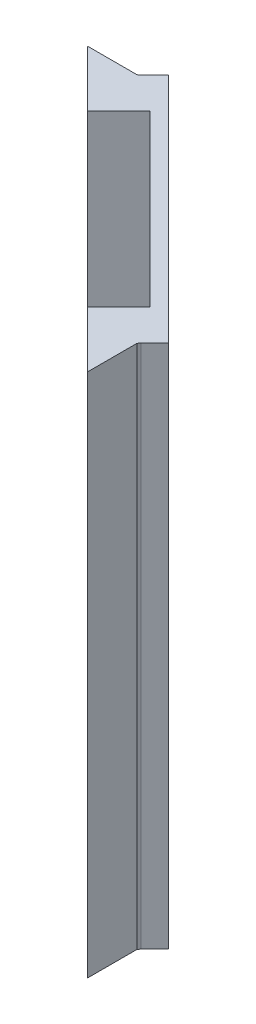
SolidWorks part; units mm, degrees
ref_plane "Front Plane" through (0, 0, 0) normal (0, 0, 1) x (1, 0, 0)
ref_plane "Top Plane" through (0, 0, 0) normal (0, 1, 0) x (1, 0, 0)
ref_plane "Right Plane" through (0, 0, 0) normal (1, 0, 0) x (0, 0, -1)
sketch "Sketch1" plane through (0, 0, 0) normal (0, 1, 0) x (1, 0, 0)
  line L1 (53.7307, 35.7377) -> (89.086, 0.3824) construction
  line L3 (89.086, -49.6176) -> (-36.2693, -49.6176) construction
  line L4 (-36.2693, -49.6176) -> (-36.2693, 35.7377) construction
  line L5 (-39.2693, -52.6176) -> (-39.2693, 38.7377) construction
  line L6 (-39.2693, 38.7377) -> (54.9733, 38.7377) construction
  line L7 (54.9733, 38.7377) -> (92.086, 1.625) construction
  line L8 (92.086, 1.625) -> (92.086, -52.6176) construction
  line L9 (92.086, -52.6176) -> (-39.2693, -52.6176) construction
  line L10 (53.7307, 35.7377) -> (55.852, 37.859) construction
  line L11 (89.086, 0.3824) -> (91.2073, 2.5037) construction
  line L12 (49.3113, 31.6718) -> (89.086, -8.1029) construction
  line L13 (53.3771, 35.7377) -> (55.6752, 38.0358) construction
  line L14 (55.6752, 38.0358) -> (54.9733, 38.7377) construction
  line L15 (91.2073, 2.5037) -> (92.086, 1.625) construction
  line L16 (89.086, 0.0288) -> (91.3841, 2.3269) construction
  line L17 (85.1969, -8.4565) -> (44.8918, 31.8486) construction
  line L18 (-36.2693, 35.7377) -> (53.3771, 35.7377) construction
  line L19 (-36.2693, 35.7377) -> (53.7307, 35.7377) construction
  line L20 (89.086, -49.6176) -> (89.086, 0.0288) construction
  line L21 (89.086, 0.3824) -> (89.086, -49.6176) construction
  line L22 (44.8918, 31.8486) -> (50.7255, 26.015) construction
  line L23 (50.7255, 26.015) -> (52.8468, 28.1363) construction
  line L24 (52.8468, 28.1363) -> (49.3113, 31.6718) construction
  line L25 (53.3771, 35.7377) -> (49.3113, 31.6718) construction
  line L26 (85.1969, -8.4565) -> (79.363, -2.6225) construction
  line L27 (79.363, -2.6225) -> (81.4843, -0.5012) construction
  line L28 (85.0198, -4.0367) -> (81.4843, -0.5012) construction
  line L29 (89.086, -8.1029) -> (89.086, 0.0288) construction
  line L30 (89.086, 0.0288) -> (85.0198, -4.0367) construction
  line L31 (49.3113, 31.6718) -> (45.2454, 35.7377) construction
  line L32 (44.8918, 31.8486) -> (51.0028, 35.7377) construction
  line L33 (85.1969, -8.4565) -> (89.086, -12.3456) construction
  line L34 (85.0198, -4.0367) -> (89.086, -8.1029) construction
  line L35 (-36.2693, 24.0809) -> (-24.6125, 35.7377) construction
  line L36 (50.7255, 26.015) -> (9.8915, 35.7377) construction
  line L37 (35.7601, 35.7377) -> (35.7601, 29.5783) construction
  line L38 (35.7601, 29.5783) -> (50.7255, 26.015) construction
  line L39 (-36.2693, -37.9608) -> (-24.6125, -49.6176) construction
  line L40 (73.5297, 20.1814) -> (65.0444, 11.6961) construction
  line L41 (89.086, -17.5882) -> (82.9266, -17.5882) construction
  line L42 (82.9266, -17.5882) -> (79.3633, -2.6228) construction
  line L43 (26.4084, -52.6176) -> (26.4084, 38.7377) construction
  line L44 (89.086, -37.9608) -> (77.4292, -49.6176) construction
  line L45 (89.086, 0.3824) -> (91.2073, 2.5037)
  line L46 (91.2073, 2.5037) -> (55.852, 37.859)
  line L47 (55.852, 37.859) -> (53.7307, 35.7377)
  line L48 (-36.2693, 35.4877) -> (53.3771, 35.4877) construction
  line L49 (49.488, 31.8486) -> (89.2628, -7.9261) construction
  line L50 (49.488, 31.8486) -> (45.4222, 35.9145) construction
  line L51 (88.836, -49.6176) -> (88.836, 0.0288) construction
  line L52 (88.836, 0.0288) -> (89.086, 0.3824)
  line L53 (53.7307, 35.7377) -> (53.3771, 35.4877)
  line L54 (53.3771, 35.4877) -> (45.8066, 35.4877)
  line L55 (45.8066, 35.4877) -> (88.836, -7.4994)
  line L56 (88.836, -7.4994) -> (88.836, 0.0288)
  circle A0 centre (-33.2693, 32.7377) radius 2 construction
  circle A1 centre (39.7601, 32.7377) radius 2 construction
  circle A2 centre (-33.2693, -46.6176) radius 2 construction
  circle A4 centre (86.086, -13.5882) radius 2 construction
  circle A5 centre (86.086, -46.6176) radius 2 construction
  dimension "D11" = 4
  dimension "D14" = 4
  dimension "D16" = 4
  dimension "D19" = 4
  dimension "D21" = 4
  dimension "D25" = 4
  dimension "D26" = 0.25
  dimension "D1" = 90
  dimension "D2" = 5
  dimension "D3" = 50
  dimension "D4" = 50
  dimension "D6" = 6
  dimension "D7" = 0.25
  dimension "D8" = 0.25
  dimension "D9" = 3
  dimension "D10" = 5
  dimension "D12" = 6
  dimension "D13" = 6
  dimension "D15" = 135
  dimension "D17" = 6
  dimension "D18" = 6
  dimension "D20" = 4
  dimension "D22" = 135
  dimension "D23" = 6
  dimension "D24" = 6
  dimension "D5" = 3
  dimension "D27" = 0.25
extrude "Boss-Extrude1" add sketch "Sketch1" along normal blind 80
sketch "Sketch2" plane through (46.8555, 0, -46.8555) normal (0.7071, 0, -0.7071) x (-0.7071, 0, -0.7071)
  line L0 (-19.473, 80) -> (-19.473, 0)
  line L1 (-62.723, 80) -> (-12.723, 80) construction
  line L2 (-62.723, 0) -> (-12.723, 0) construction
  line L3 (-55.973, 0) -> (-55.973, 80)
  line L4 (-37.723, 80) -> (-37.723, 0) construction
  line L5 (-19.473, 80) -> (-55.973, 80)
  line L6 (-19.473, 0) -> (-55.973, 0)
  dimension "D1" = 36.5
  dimension "D2" = 18.25
extrude "Cut-Extrude1" cut sketch "Sketch2" against normal blind 9
sketch "Sketch3" plane through (46.8555, 0, -46.8555) normal (0.7071, 0, -0.7071) x (-0.7071, 0, -0.7071)
  line L0 (-12.723, 80) -> (-62.723, 80)
  line L1 (-62.723, 80) -> (-62.723, 0)
  line L2 (-62.723, 0) -> (-12.723, 0)
  line L3 (-12.723, 0) -> (-12.723, 80)
  line L4 (-25.223, 76) -> (-25.223, 4)
  line L5 (-25.223, 4) -> (-50.223, 4)
  line L7 (-50.223, 4) -> (-50.223, 76)
  line L8 (-50.223, 76) -> (-25.223, 76)
  line L9 (-37.723, 80) -> (-37.723, 0) construction
  line L10 (-62.723, 40) -> (-12.723, 40) construction
  dimension "D1" = 25
  dimension "D2" = 12.5
  dimension "D3" = 72
  dimension "D4" = 36
extrude "Boss-Extrude2" add sketch "Sketch3" against normal blind 2
